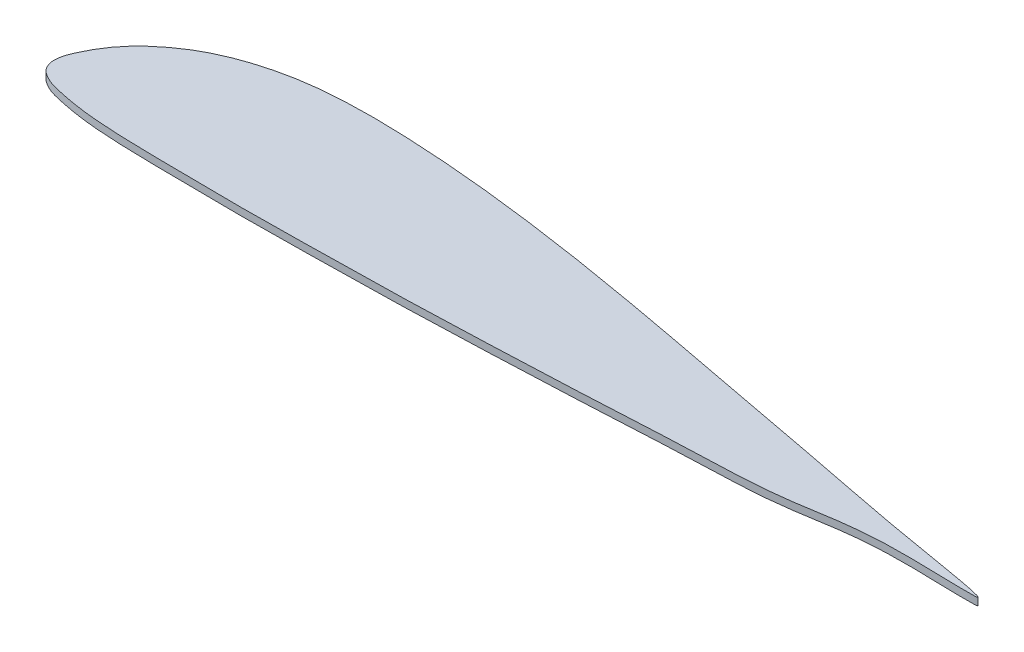
SolidWorks part; units mm, degrees
ref_plane "Front Plane" through (0, 0, 0) normal (0, 0, 1) x (1, 0, 0)
ref_plane "Top Plane" through (0, 0, 0) normal (0, 1, 0) x (1, 0, 0)
ref_plane "Right Plane" through (0, 0, 0) normal (1, 0, 0) x (0, 0, -1)
sketch "Sketch2" plane through (0, 0, 0) normal (0, 1, 0) x (1, 0, 0)
  line L0 (0, 0) -> (100, 0) construction
  spline S0 degree 3 poles (42.0873, 2.7049) (128.9004, -3.2299) (42.1189, 10.3859) (2.1126, 18.7667) (-50.5691, 28.5472) (-99.8067, 38.0388) (-149.9163, 47.244) (-199.8368, 54.8701) (-241.5928, 59.2881) (-274.9813, 61.094) (-300.0436, 61.2795) (-325.3399, 59.1576) (-347.2365, 53.586) (-363.8699, 46.3213) (-375.5293, 38.7045) (-383.8634, 31.5103) (-390.4621, 23.9229) (-394.5474, 17.588) (-398.4445, 9.7487) (-401.3735, 1.9398) (-398.3879, -4.93) (-394.3596, -7.7664) (-390.1963, -9.902) (-383.3746, -11.572) (-375.0576, -13.2576) (-363.3705, -14.8041) (-346.6865, -15.9165) (-325.0013, -16.2615) (-300.0015, -16.59) (-274.9985, -16.6786) (-241.6669, -16.1681) (-199.9773, -15.594) (-150.0315, -13.7396) (-99.8396, -11.6454) (-50.5637, -8.6765) (2.2509, -7.6445) (42.0873, 2.7049) (128.9004, -3.2299) (42.1189, 10.3859) knots -0.144975 -0.096715 -0.048179 0 0.049041 0.098082 0.147123 0.196163 0.245117 0.293835 0.342264 0.366386 0.390475 0.414675 0.439566 0.455415 0.466908 0.479712 0.48709 0.495937 0.501323 0.512663 0.51831 0.521365 0.526752 0.531755 0.541582 0.551305 0.565797 0.589895 0.613986 0.638076 0.662167 0.710354 0.75856 0.806786 0.855025 0.903285 0.951821 1 1.049041 1.098082 1.147123 only from (100, 0) to (100, 0)
  point P3 (0.5, 2.3)
  point P4 (1, 3.3)
  point P5 (2, 4.84)
  point P6 (3, 6)
  point P7 (5, 7.75)
  point P8 (7, 9.05)
  point P9 (10, 10.4)
  point P10 (15, 11.7)
  point P11 (20, 12.18)
  point P12 (25, 12.18)
  point P13 (30, 11.92)
  point P14 (40, 10.9)
  point P15 (60, -2.3)
  point P16 (50, -2.74)
  point P17 (40, -3.08)
  point P18 (30, -3.26)
  point P19 (25, -3.32)
  point P20 (20, -3.31)
  point P21 (15, -3.25)
  point P22 (10, -3.12)
  point P23 (7, -2.9)
  point P24 (5, -2.63)
  point P25 (3, -2.23)
  point P26 (2, -1.95)
  point P27 (1, -1.45)
  point P28 (0.5, -1.06)
  point P29 (50, 9.4)
  point P30 (70, 5.7)
  point P31 (60, 7.6)
  point P32 (80, 3.8)
  point P33 (90, 1.9)
  point P34 (100, 0)
  point P35 (70, -1.8)
  point P36 (80, -1.22)
  point P37 (90, -0.0001)
  dimension "D1" = 100
  dimension "D3" = 1
  dimension "D4" = 2
  dimension "D5" = 3
  dimension "D6" = 5
  dimension "D7" = 7
  dimension "D8" = 10
  dimension "D9" = 15
  dimension "D10" = 20
  dimension "D11" = 25
  dimension "D12" = 30
  dimension "D13" = 40
  dimension "D14" = 50
  dimension "D15" = 70
  dimension "D16" = 60
  dimension "D17" = 80
  dimension "D18" = 90
  dimension "D19" = 100
  dimension "D20" = 2.3
  dimension "D21" = 3.3
  dimension "D22" = 4.84
  dimension "D23" = 6
  dimension "D24" = 7.75
  dimension "D25" = 9.05
  dimension "D26" = 10.4
  dimension "D27" = 11.7
  dimension "D28" = 12.18
  dimension "D29" = 12.18
  dimension "D30" = 11.92
  dimension "D31" = 10.9
  dimension "D32" = 9.4
  dimension "D33" = 7.6
  dimension "D34" = 5.7
  dimension "D35" = 3.8
  dimension "D36" = 1.9
  dimension "D37" = 0
  dimension "D38" = 0.5
  dimension "D39" = 1.06
  dimension "D40" = 1.45
  dimension "D41" = 1.95
  dimension "D42" = 2.23
  dimension "D43" = 2.63
  dimension "D44" = 2.9
  dimension "D45" = 3.12
  dimension "D46" = 3.25
  dimension "D47" = 3.31
  dimension "D48" = 3.32
  dimension "D49" = 3.26
  dimension "D50" = 3.08
  dimension "D51" = 2.74
  dimension "D52" = 2.3
  dimension "D53" = 1.8
  dimension "D54" = 1.22
  dimension "D55" = 0.0001
extrude "Boss-Extrude3" add sketch "Sketch2" along normal blind 4 contours S0
